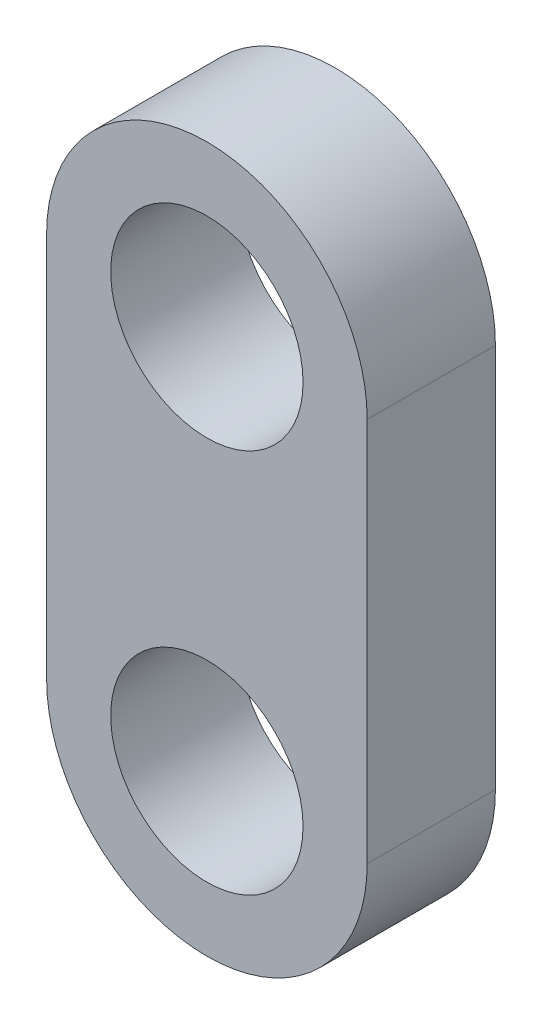
SolidWorks part; units mm, degrees
ref_plane "Front Plane" through (0, 0, 0) normal (0, 0, 1) x (1, 0, 0)
ref_plane "Top Plane" through (0, 0, 0) normal (0, 1, 0) x (1, 0, 0)
ref_plane "Right Plane" through (0, 0, 0) normal (1, 0, 0) x (0, 0, -1)
sketch "Sketch1" plane through (0, 0, 0) normal (0, 0, 1) x (1, 0, 0)
  line L0 (0, -15) -> (0, 15) construction
  line L1 (-12.5, -15) -> (-12.5, 15)
  line L2 (12.5, -15) -> (12.5, 15)
  arc A0 (-12.5, -15) -> (12.5, -15) centre (0, -15) ccw
  arc A1 (12.5, 15) -> (-12.5, 15) centre (0, 15) ccw
  circle A2 centre (0, 15) radius 7.5
  circle A3 centre (0, -15) radius 7.5
  point P3 (0, 0)
  dimension "D3" = 15
  dimension "D1" = 25
  dimension "D2" = 30
extrude "Boss-Extrude1" add sketch "Sketch1" along normal blind 10
